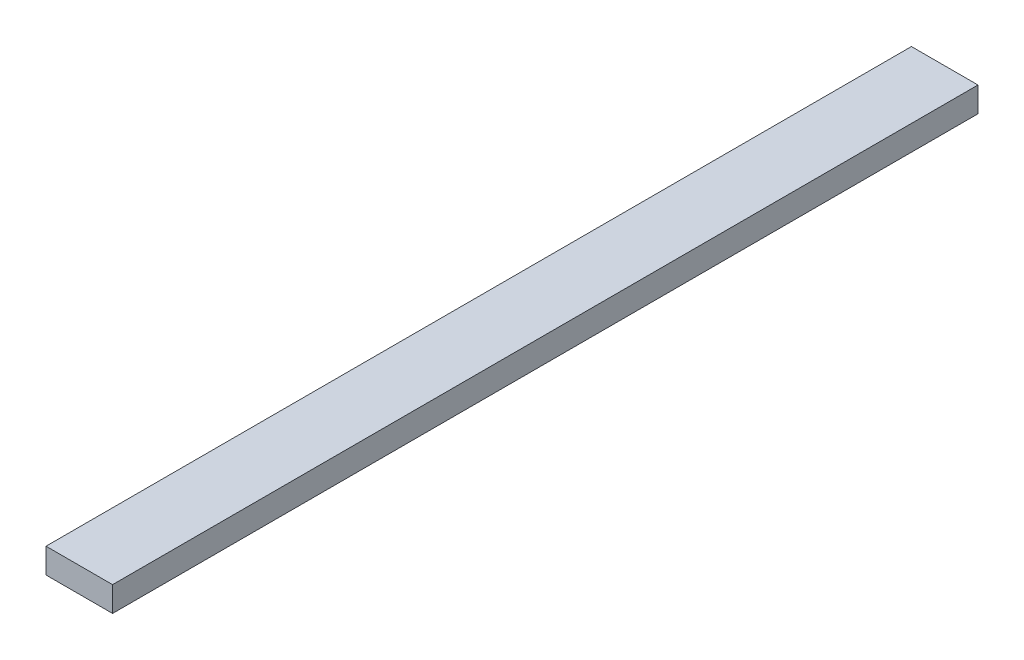
SolidWorks part; units mm, degrees
ref_plane "Plane1" through (0, 0, 0) normal (0, 0, 1) x (1, 0, 0)
ref_plane "Plane2" through (0, 0, 0) normal (0, 1, 0) x (1, 0, 0)
ref_plane "Plane3" through (0, 0, 0) normal (1, 0, 0) x (0, 0, -1)
sketch "Sketch1" plane through (0, 0, 0) normal (0, 1, 0) x (1, 0, 0)
  line L1 (0, 0) -> (40, 0)
  line L2 (0, 0) -> (0, 520)
  line L3 (0, 520) -> (40, 520)
  line L4 (40, 0) -> (40, 520)
  dimension "D1" = 520
  dimension "D2" = 40
extrude "Boss-Extrude2" add sketch "Sketch1" along normal blind 15
